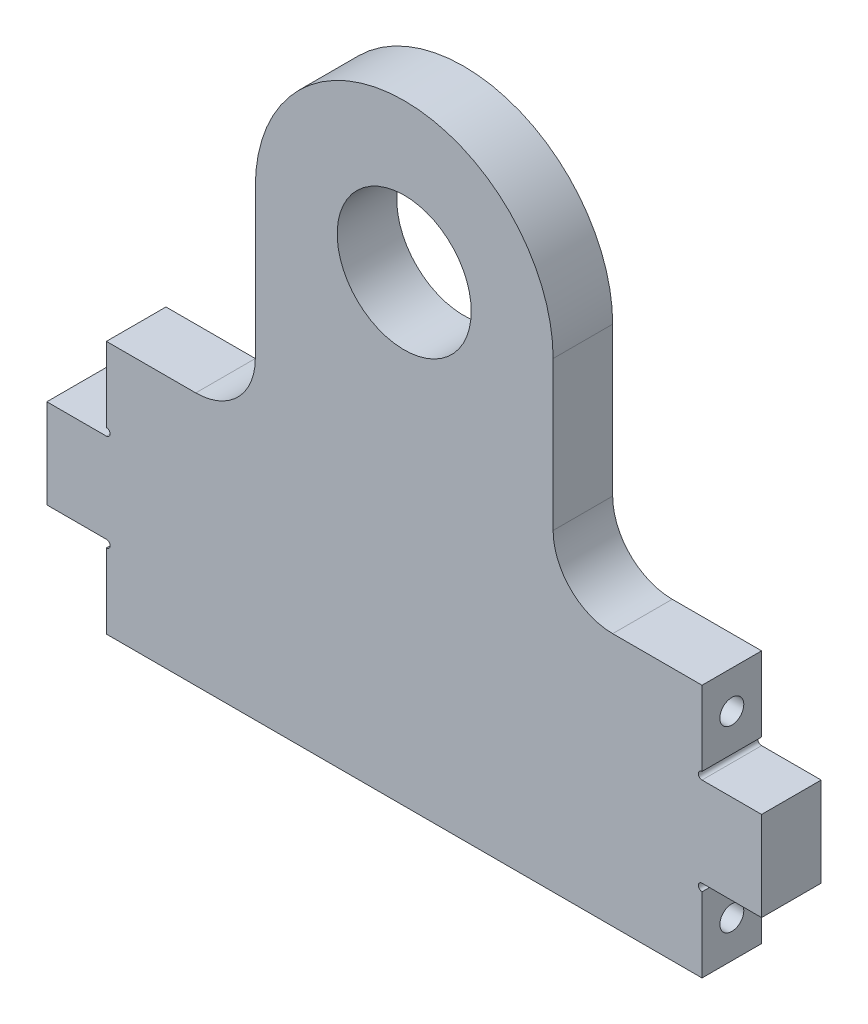
SolidWorks part; units mm, degrees
material "6061-T6 (SS)"
ref_plane "Front Plane" through (0, 0, 0) normal (0, 0, 1) x (1, 0, 0)
ref_plane "Top Plane" through (0, 0, 0) normal (0, 1, 0) x (1, 0, 0)
ref_plane "Right Plane" through (0, 0, 0) normal (1, 0, 0) x (0, 0, -1)
sketch "Sketch1" plane through (0, 0, 0) normal (0, 0, 1) x (1, 0, 0)
  line L1 (-63.5, 0) -> (63.5, 0)
  line L2 (-63.5, 0) -> (-63.5, 152.4)
  line L3 (-63.5, 152.4) -> (63.5, 152.4)
  line L4 (63.5, 0) -> (63.5, 152.4)
  dimension "D1" = 127
  dimension "D2" = 152.4
extrude "Boss-Extrude1" add sketch "Sketch1" along normal blind 12.7
sketch "Sketch2" plane through (0, 0, 12.7) normal (0, 0, 1) x (1, 0, 0)
  line L0 (31.75, 95.25) -> (31.75, 50.8)
  line L1 (31.75, 50.8) -> (63.5, 50.8)
  line L2 (63.5, 0) -> (63.5, 152.4) construction
  line L3 (63.5, 50.8) -> (63.5, 152.4)
  line L4 (63.5, 152.4) -> (-63.5, 152.4)
  line L5 (-63.5, 152.4) -> (-63.5, 50.8)
  line L6 (-63.5, 152.4) -> (-63.5, 0) construction
  line L7 (-63.5, 50.8) -> (-31.75, 50.8)
  line L8 (-31.75, 50.8) -> (-31.75, 95.25)
  line L9 (-63.5, 0) -> (63.5, 0) construction
  circle A0 centre (0, 95.25) radius 14.2875
  arc A1 (31.75, 95.25) -> (-31.75, 95.25) centre (0, 95.25) ccw
  dimension "D1" = 28.575
  dimension "D2" = 63.5
  dimension "D3" = 50.8
extrude "Cut-Extrude1" cut sketch "Sketch2" against normal through all
fillet "Fillet1" radius 12.7 2 edges at (-31.75, 50.8, 6.35) (31.75, 50.8, 6.35)
sketch "Sketch3" plane through (0, 0, 12.7) normal (0, 0, 1) x (1, 0, 0)
  line L1 (-63.5, 0) -> (63.5, 0)
  line L2 (-63.5, 0) -> (-63.5, -3.2615)
  line L3 (-63.5, -3.2615) -> (63.5, -3.2615)
  line L4 (63.5, 0) -> (63.5, -3.2615)
extrude "Boss-Extrude2" add sketch "Sketch3" against normal blind 12.7
hole_wizard "1/4-20 Tapped Hole1" positions "Sketch5" profile "Sketch4" tap size "1/4-20" standard "ANSI Inch"
sketch "Sketch5" plane through (63.5, 0, 0) normal (1, 0, 0) x (0, 0, -1)
  line L0 (-12.7, 23.7693) -> (0, 23.7693) construction
  line L1 (-12.7, -3.2615) -> (-12.7, 50.8) construction
  line L2 (0, -3.2615) -> (0, 50.8) construction
  line L4 (-6.35, 42.8193) -> (-6.35, 23.7693) construction
  line L5 (-6.35, 23.7693) -> (-6.35, 4.7193) construction
  point P0 (-6.35, 42.8193)
  point P2 (-6.35, 4.7193)
  dimension "D1" = 19.05
sketch "Sketch4" plane through (63.5, 42.8193, 6.35) normal (0, 1, 0) x (0, 0, -1)
  line L0 (0, 0) -> (0, 18.0438)
  line L1 (0, 18.0438) -> (2.5527, 16.51)
  line L2 (2.5527, 16.51) -> (2.5527, 0)
  line L5 (2.5527, 0) -> (0, 0)
  line L10 (0, 18.0438) -> (-2.5527, 16.51) construction
  line L11 (0, -6.35) -> (0, 107.95) construction
  dimension "Tap Drill Dia." = 5.1054
  dimension "Tap Drill Depth" = 16.51
  dimension "Drill Angle" = 118
sketch "Sketch6" plane through (63.5, 0, 0) normal (1, 0, 0) x (0, 0, -1)
  line L0 (-12.7, -3.2615) -> (-12.7, 50.8) construction
  line L1 (-12.7, 33.2943) -> (0, 33.2943)
  line L2 (-12.7, 33.2943) -> (-12.7, 14.2443)
  line L3 (-12.7, 14.2443) -> (0, 14.2443)
  line L4 (0, 33.2943) -> (0, 14.2443)
  line L5 (0, -3.2615) -> (0, 50.8) construction
  point P8 (0, 23.7693)
  dimension "D1" = 19.05
extrude "Boss-Extrude3" add sketch "Sketch6" along normal blind 12.7
sketch "Sketch7" plane through (0, 0, 12.7) normal (0, 0, 1) x (1, 0, 0)
  line L0 (63.5, 33.2943) -> (63.5, 50.8) construction
  line L1 (63.5, -3.2615) -> (63.5, 14.2443) construction
  circle A0 centre (63.5, 34.088) radius 0.7937
  circle A1 centre (63.5, 13.4505) radius 0.7937
  dimension "D1" = 1.5875
extrude "Cut-Extrude2" cut sketch "Sketch7" against normal through all
mirror "Mirror1" about plane through (0, 0, 0) normal (1, 0, 0) of "Cut-Extrude2", "Boss-Extrude3", "1/4-20 Tapped Hole1"
